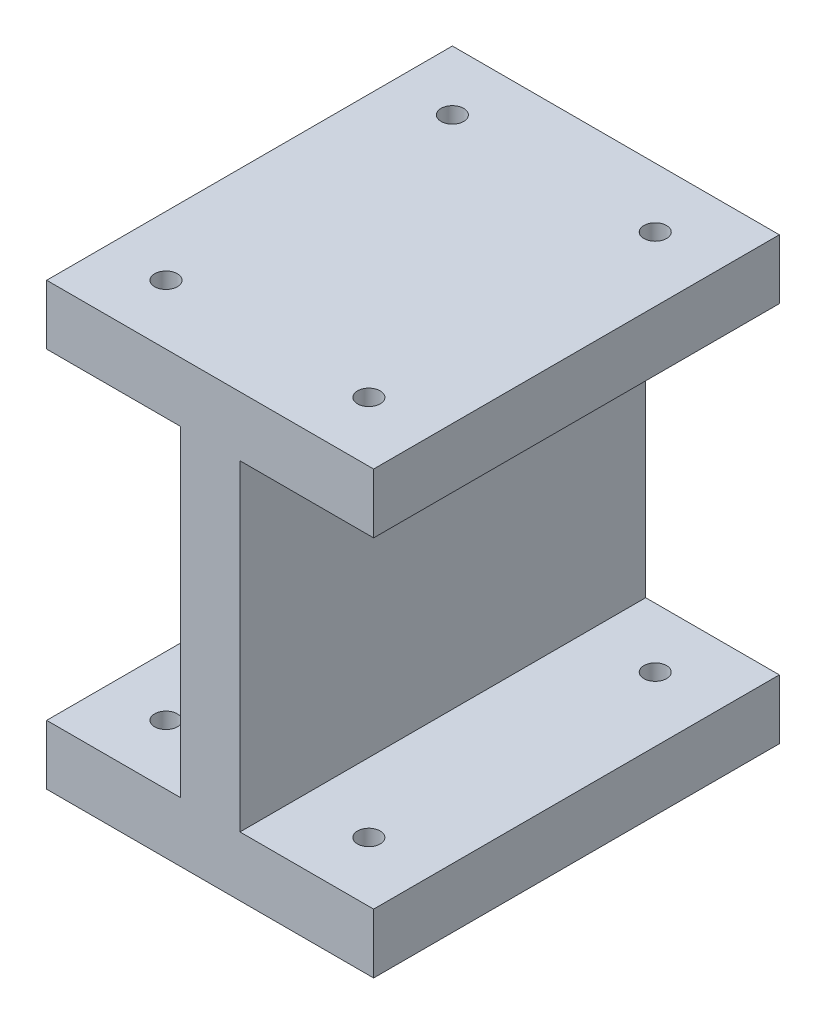
SolidWorks part; units mm, degrees
material "ABS"
ref_plane "Front Plane" through (0, 0, 0) normal (0, 0, 1) x (1, 0, 0)
ref_plane "Top Plane" through (0, 0, 0) normal (0, 1, 0) x (1, 0, 0)
ref_plane "Right Plane" through (0, 0, 0) normal (1, 0, 0) x (0, 0, -1)
sketch "Sketch1" plane through (0, 0, 0) normal (0, 0, 1) x (1, 0, 0)
  line L1 (0, 0) -> (34.798, 0)
  line L2 (0, 0) -> (0, 46.9138)
  line L3 (0, 46.9138) -> (34.798, 46.9138)
  line L4 (34.798, 0) -> (34.798, 46.9138)
  line L5 (0, 0) -> (34.798, 46.9138) construction
  line L6 (0, 46.9138) -> (34.798, 0) construction
  point P4 (17.399, 23.4569)
  dimension "D1" = 46.9138
  dimension "D2" = 34.798
extrude "Boss-Extrude1" add sketch "Sketch1" against normal blind 43.18
sketch "Sketch2" plane through (0, 0, 0) normal (0, 0, 1) x (1, 0, 0)
  line L0 (0, 46.9138) -> (0, 0) construction
  line L1 (0, 6.35) -> (14.224, 6.35)
  line L2 (0, 6.35) -> (0, 40.5638)
  line L3 (0, 40.5638) -> (14.224, 40.5638)
  line L4 (14.224, 6.35) -> (14.224, 40.5638)
  line L5 (0, 6.35) -> (14.224, 40.5638) construction
  line L6 (0, 40.5638) -> (14.224, 6.35) construction
  line L7 (34.798, 0) -> (34.798, 46.9138) construction
  line L8 (20.574, 40.5638) -> (34.798, 40.5638)
  line L9 (20.574, 40.5638) -> (20.574, 6.35)
  line L10 (20.574, 6.35) -> (34.798, 6.35)
  line L11 (34.798, 40.5638) -> (34.798, 6.35)
  line L12 (20.574, 40.5638) -> (34.798, 6.35) construction
  line L13 (20.574, 6.35) -> (34.798, 40.5638) construction
  line L14 (34.798, 46.9138) -> (0, 46.9138) construction
  line L15 (0, 0) -> (34.798, 0) construction
  point P4 (7.112, 23.4569)
  point P11 (27.686, 23.4569)
  dimension "D1" = 6.35
  dimension "D2" = 6.35
  dimension "D3" = 6.35
extrude "Cut-Extrude1" cut sketch "Sketch2" against normal blind 43.18
sketch "Sketch3" plane through (0, 46.9138, 0) normal (0, 1, 0) x (1, 0, 0)
  circle A1 centre (6.35, 6.35) radius 1.2065
  circle A3 centre (27.94, 6.35) radius 1.2065
  circle A5 centre (6.35, 36.83) radius 1.2065
  circle A7 centre (27.94, 36.83) radius 1.2065
  dimension "D1" = 2.413
extrude "Cut-Extrude2" cut sketch "Sketch3" against normal through all
